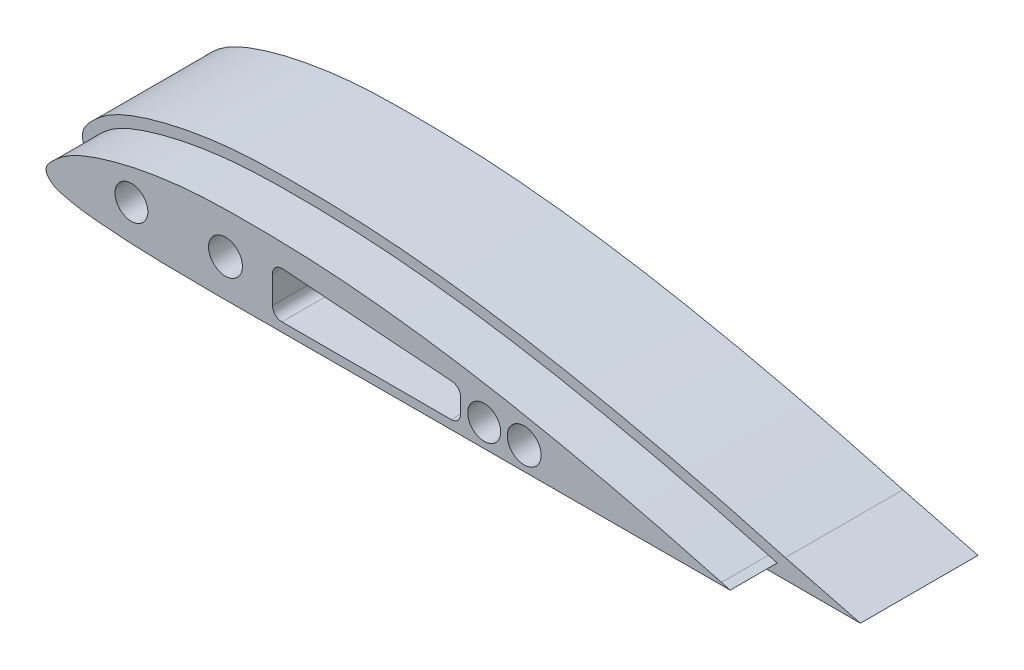
SolidWorks part; units mm, degrees
ref_plane "Front Plane" through (0, 0, 0) normal (0, 0, 1) x (1, 0, 0)
ref_plane "Top Plane" through (0, 0, 0) normal (0, 1, 0) x (1, 0, 0)
ref_plane "Right Plane" through (0, 0, 0) normal (1, 0, 0) x (0, 0, -1)
sketch "Sketch1" plane through (0, 0, 0) normal (0, 0, 1) x (1, 0, 0)
  line L4 (283.5115, 5) -> (300, 5)
  line L5 (300, 5) -> (284.0429, 9.1047)
  spline S2 degree 3 poles (284.0429, 9.1047) (281.0182, 9.9344) (274.9702, 11.5879) (262.7947, 14.6943) (247.4912, 18.2235) (228.9768, 21.8279) (213.3822, 24.0502) (200.838, 25.2782) (191.3752, 25.8437) (181.9292, 26.0327) (174.0455, 26.006) (167.6846, 25.6725) (162.9071, 25.1908) (158.1715, 24.4731) (154.2495, 23.6877) (151.1262, 22.9144) (148.8034, 22.2534) (146.5027, 21.5203) (144.1955, 20.6739) (142.2855, 19.8254) (140.7789, 19.0238) (139.6571, 18.333) (138.5799, 17.556) (137.5736, 16.6946) (136.8402, 16.0177) (136.1979, 15.3779) (135.7035, 14.8191) (135.2097, 14.1357) (134.8343, 13.4013) (134.6172, 12.6132) (134.5644, 11.9259) (134.6325, 11.2839) (134.8239, 10.646) (135.0503, 10.1715) (135.4024, 9.5941) (135.889, 9.014) (136.5032, 8.4537) (137.1891, 7.9612) (137.9344, 7.5673) (138.8878, 7.188) (139.9999, 6.8937) (141.1193, 6.6336) (142.3398, 6.3625) (143.5667, 6.1418) (145.2014, 5.9056) (147.2085, 5.702) (149.5549, 5.5018) (152.7201, 5.2635) (156.6645, 5.0546) (161.3946, 4.9004) (166.1151, 4.8221) (170.8269, 4.7935) (175.5318, 4.7968) (181.7926, 4.8194) (189.6121, 4.8333) (199.0042, 4.8461) (208.3936, 4.8645) (217.7834, 4.8816) (230.303, 4.9047) (245.9523, 4.9321) (264.7317, 4.9664) (277.2516, 4.9881) (283.5115, 5) knots 0 0 0 0 0.03125 0.0625 0.125 0.1875 0.25 0.28125 0.3125 0.34375 0.375 0.390625 0.40625 0.421875 0.4375 0.445312 0.453125 0.460938 0.46875 0.476562 0.480469 0.484375 0.488281 0.492188 0.496094 0.498047 0.5 0.501953 0.503906 0.504883 0.505859 0.506836 0.507812 0.508789 0.509766 0.511719 0.513672 0.515625 0.517578 0.519531 0.523438 0.527344 0.53125 0.535156 0.539062 0.546875 0.554688 0.5625 0.578125 0.59375 0.609375 0.625 0.640625 0.65625 0.6875 0.71875 0.75 0.78125 0.8125 0.875 0.9375 1 1 1 1
extrude "Boss-Extrude1" add sketch "Sketch1" along normal blind 25
sketch "Sketch2" plane through (0, 0, 25) normal (0, 0, 1) x (1, 0, 0)
  line L0 (283.5138, 7.176) -> (283.5077, 7)
  spline S1 degree 3 poles (283.5138, 7.176) (281.5719, 7.7087) (278.6602, 8.5075) (273.8037, 9.8057) (267.9783, 11.312) (262.1421, 12.7496) (255.3336, 14.3496) (248.5296, 15.8732) (237.8298, 18.0745) (225.1769, 20.3734) (211.4981, 22.2445) (201.7081, 23.1823) (192.8989, 23.7583) (187.0194, 23.95) (180.1574, 24.0138) (175.2497, 24.0043) (170.3385, 23.8312) (165.4154, 23.4617) (161.4718, 22.9737) (156.5308, 22.1318) (152.5638, 21.2602) (148.6188, 20.1142) (145.6144, 19.0989) (143.118, 18.0296) (141.124, 16.9205) (139.7091, 15.9185) (138.6393, 14.9581) (137.8213, 14.1846) (137.2992, 13.6166) (136.9099, 13.0649) (136.6947, 12.6285) (136.5581, 12.111) (136.5906, 11.6817) (136.7264, 11.3043) (136.876, 11.0027) (137.1856, 10.5599) (137.6647, 10.0852) (138.4186, 9.5356) (139.4995, 9.074) (140.8875, 8.7436) (142.3453, 8.4004) (143.8077, 8.1247) (145.7594, 7.8486) (148.2057, 7.6221) (151.1393, 7.3799) (157.0097, 7.007) (166.8124, 6.7551) (180.539, 6.8235) (193.287, 6.8363) (208.9776, 6.8654) (224.6681, 6.8944) (240.3587, 6.9228) (251.1459, 6.9412) (259.9719, 6.958) (268.7978, 6.973) (276.6431, 6.9879) (281.5464, 6.9963) (283.5077, 7) knots 0 0 0 0 0.020105 0.030145 0.050191 0.08018 0.090156 0.12002 0.149793 0.199219 0.248396 0.287604 0.297393 0.336535 0.346322 0.365908 0.385531 0.395376 0.415192 0.425184 0.445412 0.455711 0.466191 0.477055 0.482787 0.488946 0.494316 0.497126 0.500187 0.502001 0.50385 0.50502 0.507318 0.507987 0.509024 0.510668 0.513358 0.515716 0.519949 0.524973 0.529954 0.534903 0.539824 0.54963 0.559425 0.569214 0.608356 0.657307 0.706263 0.735637 0.813967 0.862923 0.892297 0.92167 0.951044 0.980418 1 1 1 1
extrude "Boss-Extrude2" add sketch "Sketch2" along normal blind 10
sketch "Sketch4" plane through (0, 0, 35) normal (0, 0, 1) x (1, 0, 0)
  line L0 (300, 5) -> (88.4314, 5) construction
  circle A0 centre (175, 15) radius 3.6
  circle A1 centre (238.5138, 12) radius 3.6
  dimension "D2" = 125
  dimension "D3" = 45
  dimension "D4" = 7
  dimension "D1" = 10
extrude "Cut-Extrude1" cut sketch "Sketch4" against normal blind 15 contours A0 | A1
sketch "Sketch5" plane through (0, 0, 35) normal (0, 0, 1) x (1, 0, 0)
  line L0 (185, 19) -> (185, 9)
  line L1 (185, 9) -> (225, 9)
  line L2 (225, 9) -> (225, 16)
  line L3 (225, 16) -> (185, 19)
  line L4 (300, 5) -> (100, 5) construction
  dimension "D1" = 10
  dimension "D2" = 4
  dimension "D3" = 7
  dimension "D4" = 75
  dimension "D5" = 40
extrude "Cut-Extrude3" cut sketch "Sketch5" against normal through all
fillet "Fillet1" radius 2 4 edges at (185, 19, 17.5) (185, 9, 17.5) (225, 16, 17.5) (225, 9, 17.5)
sketch "Sketch7" plane through (0, 0, 20) normal (0, 0, 1) x (1, 0, 0)
  circle A0 centre (238.5138, 12) radius 3.6 construction
  circle A1 centre (238.5138, 12) radius 3.6
  circle A2 centre (175, 15) radius 3.6
extrude "Cut-Extrude5" cut sketch "Sketch7" against normal blind 10
ref_plane "Plane1" through (160, 0, 0) normal (1, 0, 0) x (0, 0, -1)
sketch "Sketch8" plane through (160, 0, 0) normal (1, 0, 0) x (0, 0, -1)
  line L0 (-28.294, 31.7375) -> (0, 15.4019)
  line L2 (0, 4.7961) -> (0, 26.0077) construction
  line L3 (0, 15.4019) -> (-20.6135, 15.4019) construction
  dimension "D1" = 30
ref_plane "Plane2" through (160, 31.7375, 28.294) normal (0, -0.5, -0.866) x (-1, 0, 0)
sketch "Sketch11" plane through (0, 0, 35) normal (0, 0, 1) x (1, 0, 0)
  line L0 (280.5134, 7.2445) -> (282.3112, 7.2477)
  line L3 (280.448, 7.7565) -> (282.3112, 7.2477)
  line L6 (283.5115, 5) -> (300, 5)
  line L7 (300, 5) -> (284.0429, 9.1047)
  line L8 (283.5115, 5) -> (300, 5)
  line L9 (300, 5) -> (284.0429, 9.1047)
  spline S2 degree 3 poles (2469.1253, 3330.2831) (578.7241, -152.5431) (439.4264, -30.371) (262.7947, 14.6943) (247.4912, 18.2235) (228.9768, 21.8279) (213.3822, 24.0502) (200.838, 25.2782) (191.3752, 25.8437) (181.9292, 26.0327) (174.0455, 26.006) (167.6846, 25.6725) (162.9071, 25.1908) (158.1715, 24.4731) (154.2495, 23.6877) (151.1262, 22.9144) (148.8034, 22.2534) (146.5027, 21.5203) (144.1955, 20.6739) (142.2855, 19.8254) (140.7789, 19.0238) (139.6571, 18.333) (138.5799, 17.556) (137.5736, 16.6946) (136.8402, 16.0177) (136.1979, 15.3779) (135.7035, 14.8191) (135.2097, 14.1357) (134.8343, 13.4013) (134.6172, 12.6132) (134.5644, 11.9259) (134.6325, 11.2839) (134.8239, 10.646) (135.0503, 10.1715) (135.4024, 9.5941) (135.889, 9.014) (136.5032, 8.4537) (137.1891, 7.9612) (137.9344, 7.5673) (138.8878, 7.188) (139.9999, 6.8937) (141.1193, 6.6336) (142.3398, 6.3625) (143.5667, 6.1418) (145.2014, 5.9056) (147.2085, 5.702) (149.5549, 5.5018) (152.7201, 5.2635) (156.6645, 5.0546) (161.3946, 4.9004) (166.1151, 4.8221) (170.8269, 4.7935) (175.5318, 4.7968) (181.7926, 4.8194) (189.6121, 4.8333) (199.0042, 4.8461) (208.3936, 4.8645) (217.7834, 4.8816) (230.303, 4.9047) (245.9523, 4.9321) (1062.3632, 6.4244) (1873.6845, 2.8543) (2454.3014, 2917.181) knots -1.688391 -1.688391 -1.688391 -1.688391 0.03125 0.0625 0.125 0.1875 0.25 0.28125 0.3125 0.34375 0.375 0.390625 0.40625 0.421875 0.4375 0.445312 0.453125 0.460938 0.46875 0.476562 0.480469 0.484375 0.488281 0.492188 0.496094 0.498047 0.5 0.501953 0.503906 0.504883 0.505859 0.506836 0.507812 0.508789 0.509766 0.511719 0.513672 0.515625 0.517578 0.519531 0.523438 0.527344 0.53125 0.535156 0.539062 0.546875 0.554688 0.5625 0.578125 0.59375 0.609375 0.625 0.640625 0.65625 0.6875 0.71875 0.75 0.78125 0.8125 0.875 0.9375 8.963818 8.963818 8.963818 8.963818 only from (284.0429, 9.1047) to (283.5115, 5)
  spline S3 degree 3 poles (280.448, 7.7565) (274.5345, 9.3714) (262.6663, 12.4565) (244.7251, 16.5) (229.6665, 19.3599) (217.5457, 21.1803) (208.4198, 22.2922) (199.2672, 23.1416) (190.0905, 23.6336) (180.8981, 23.7894) (173.2386, 23.7336) (167.1292, 23.3697) (162.5678, 22.8749) (158.0342, 22.1607) (153.5392, 21.2365) (149.8525, 20.2348) (146.9452, 19.2923) (144.8035, 18.4896) (142.7255, 17.5469) (141.0857, 16.5987) (139.8698, 15.7033) (139.0136, 14.961) (138.1704, 14.1822) (137.4011, 13.3736) (136.8033, 12.4442) (136.8299, 11.4518) (137.4826, 10.5655) (138.3295, 9.8695) (139.3297, 9.4073) (140.4153, 9.1074) (141.5373, 8.8472) (143.0221, 8.5123) (144.8994, 8.2037) (147.177, 7.9637) (149.4676, 7.7672) (152.5195, 7.5313) (156.3422, 7.3214) (160.9342, 7.1629) (165.53, 7.0792) (171.6595, 7.0342) (179.3241, 7.0622) (188.5242, 7.0825) (197.7228, 7.0937) (209.9881, 7.1177) (225.3196, 7.1455) (243.7176, 7.1784) (262.1155, 7.2115) (274.3808, 7.2336) (280.5134, 7.2445) knots 0.010352 0.010352 0.010352 0.010352 0.071582 0.132813 0.194043 0.224658 0.255273 0.285888 0.316503 0.347118 0.377734 0.393041 0.408349 0.423656 0.438964 0.454271 0.461925 0.469579 0.477233 0.484887 0.488713 0.49254 0.496367 0.500194 0.504021 0.507848 0.511675 0.515502 0.519329 0.523155 0.526982 0.530809 0.538463 0.546117 0.553771 0.561424 0.576732 0.592039 0.607347 0.622655 0.65327 0.683885 0.7145 0.745115 0.806345 0.867576 0.928806 0.990036 0.990036 0.990036 0.990036
  spline S4 degree 3 poles (284.0429, 9.1047) (281.0182, 9.9344) (274.9702, 11.5879) (262.7947, 14.6943) (247.4912, 18.2235) (228.9768, 21.8279) (213.3822, 24.0502) (200.838, 25.2782) (191.3752, 25.8437) (181.9292, 26.0327) (174.0455, 26.006) (167.6846, 25.6725) (162.9071, 25.1908) (158.1715, 24.4731) (154.2495, 23.6877) (151.1262, 22.9144) (148.8034, 22.2534) (146.5027, 21.5203) (144.1955, 20.6739) (142.2855, 19.8254) (140.7789, 19.0238) (139.6571, 18.333) (138.5799, 17.556) (137.5736, 16.6946) (136.8402, 16.0177) (136.1979, 15.3779) (135.7035, 14.8191) (135.2097, 14.1357) (134.8343, 13.4013) (134.6172, 12.6132) (134.5644, 11.9259) (134.6325, 11.2839) (134.8239, 10.646) (135.0503, 10.1715) (135.4024, 9.5941) (135.889, 9.014) (136.5032, 8.4537) (137.1891, 7.9612) (137.9344, 7.5673) (138.8878, 7.188) (139.9999, 6.8937) (141.1193, 6.6336) (142.3398, 6.3625) (143.5667, 6.1418) (145.2014, 5.9056) (147.2085, 5.702) (149.5549, 5.5018) (152.7201, 5.2635) (156.6645, 5.0546) (161.3946, 4.9004) (166.1151, 4.8221) (170.8269, 4.7935) (175.5318, 4.7968) (181.7926, 4.8194) (189.6121, 4.8333) (199.0042, 4.8461) (208.3936, 4.8645) (217.7834, 4.8816) (230.303, 4.9047) (245.9523, 4.9321) (264.7317, 4.9664) (277.2516, 4.9881) (283.5115, 5) knots 0 0 0 0 0.03125 0.0625 0.125 0.1875 0.25 0.28125 0.3125 0.34375 0.375 0.390625 0.40625 0.421875 0.4375 0.445312 0.453125 0.460938 0.46875 0.476562 0.480469 0.484375 0.488281 0.492188 0.496094 0.498047 0.5 0.501953 0.503906 0.504883 0.505859 0.506836 0.507812 0.508789 0.509766 0.511719 0.513672 0.515625 0.517578 0.519531 0.523438 0.527344 0.53125 0.535156 0.539062 0.546875 0.554688 0.5625 0.578125 0.59375 0.609375 0.625 0.640625 0.65625 0.6875 0.71875 0.75 0.78125 0.8125 0.875 0.9375 1 1 1 1
  dimension "D1" = 0
extrude "Cut-Extrude8" cut sketch "Sketch11" against normal up to surface (10 mm away) up to face at (289.2734, 7.0524, 25)
sketch "Sketch12" plane through (0, 0, 0) normal (0, 0, -1) x (-1, 0, 0)
  circle A0 centre (-155, 15) radius 3
  circle A3 centre (-230.0138, 12) radius 3
extrude "Cut-Extrude9" cut sketch "Sketch12" against normal through all
sketch "Sketch13" plane through (0, 0, 35) normal (0, 0, 1) x (1, 0, 0)
  circle A0 centre (155, 15) radius 3.5
  circle A1 centre (230.0138, 12) radius 3.5
extrude "Cut-Extrude10" cut sketch "Sketch13" against normal blind 10
